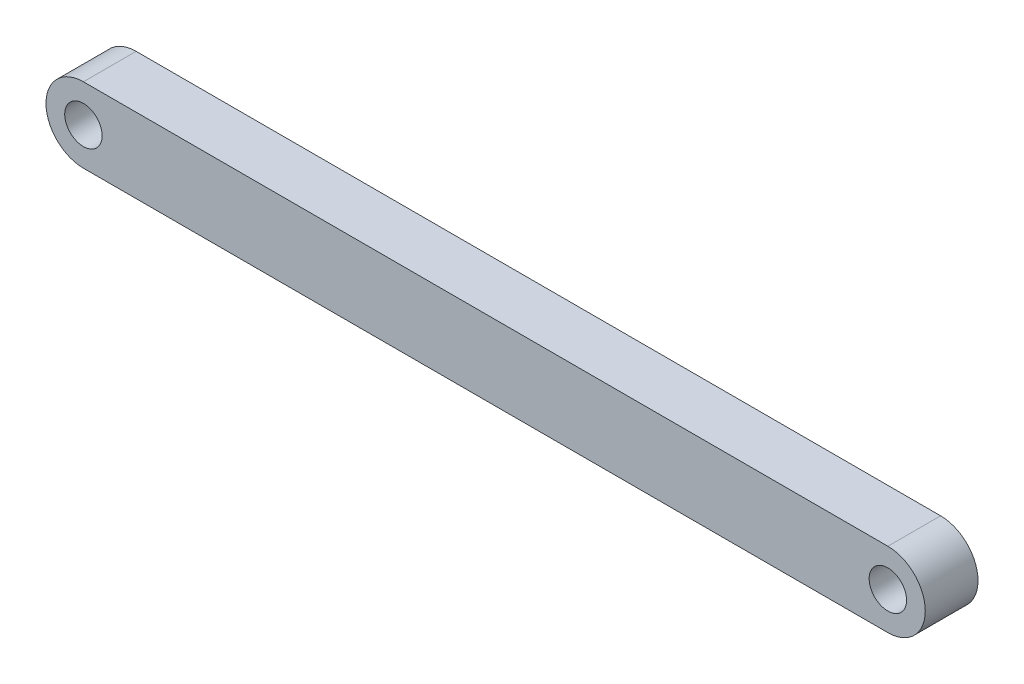
SolidWorks part; units mm, degrees
ref_plane "Front Plane" through (0, 0, 0) normal (0, 0, 1) x (1, 0, 0)
ref_plane "Top Plane" through (0, 0, 0) normal (0, 1, 0) x (1, 0, 0)
ref_plane "Right Plane" through (0, 0, 0) normal (1, 0, 0) x (0, 0, -1)
sketch "Sketch1" plane through (0, 0, 0) normal (0, 0, 1) x (1, 0, 0)
  line L0 (-38.15, 0) -> (0, 0) construction
  line L1 (-38.15, 1.775) -> (0, 1.775)
  line L2 (-38.15, -1.775) -> (0, -1.775)
  circle A0 centre (0, 0) radius 0.8875
  circle A1 centre (-38.15, 0) radius 0.8875
  arc A2 (-38.15, 1.775) -> (-38.15, -1.775) centre (-38.15, 0) ccw
  arc A3 (0, -1.775) -> (0, 1.775) centre (0, 0) ccw
  point P3 (-19.075, 0)
  dimension "D1" = 1.775
  dimension "D3" = 1.775
  dimension "D4" = 19.075
  dimension "D2" = 2
extrude "Boss-Extrude1" add sketch "Sketch1" along normal blind 2.5
